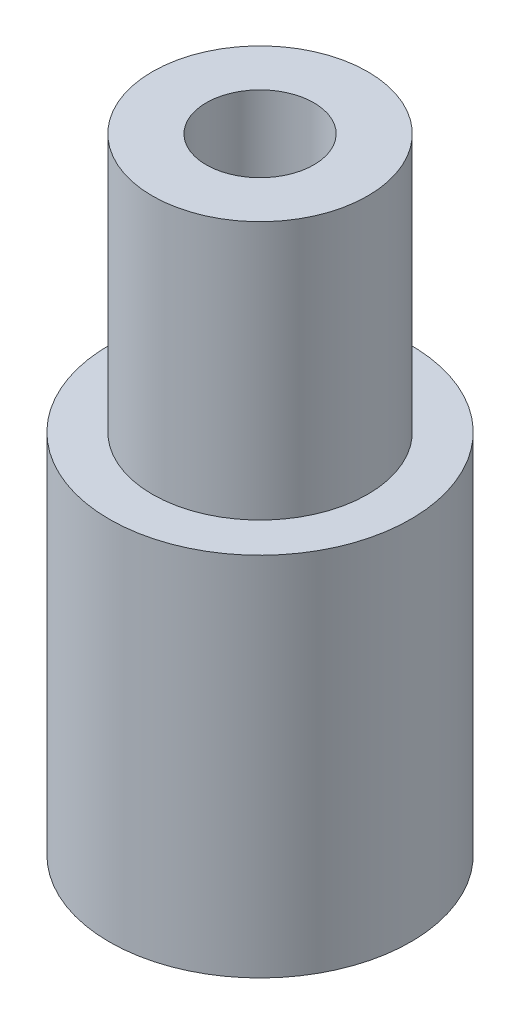
SolidWorks part; units mm, degrees
material "Cast Alloy Steel"
ref_plane "Front Plane" through (0, 0, 0) normal (0, 0, 1) x (1, 0, 0)
ref_plane "Top Plane" through (0, 0, 0) normal (0, 1, 0) x (1, 0, 0)
ref_plane "Right Plane" through (0, 0, 0) normal (1, 0, 0) x (0, 0, -1)
sketch "Sketch1" plane through (0, 0, 0) normal (0, 1, 0) x (1, 0, 0)
  circle A0 centre (0, 0) radius 7
extrude "Boss-Extrude1" add sketch "Sketch1" along normal blind 17
sketch "Sketch2" plane through (0, 17, 0) normal (0, 1, 0) x (1, 0, 0)
  circle A0 centre (0, 0) radius 5
extrude "Boss-Extrude2" add sketch "Sketch2" along normal blind 12
sketch "Sketch3" plane through (0, 29, 0) normal (0, 1, 0) x (1, 0, 0)
  circle A0 centre (0, 0) radius 2.5
extrude "Cut-Extrude1" cut sketch "Sketch3" against normal blind 14
cosmetic thread "Cosmetic Thread1" parameters "D1"=5, "D2"=6
